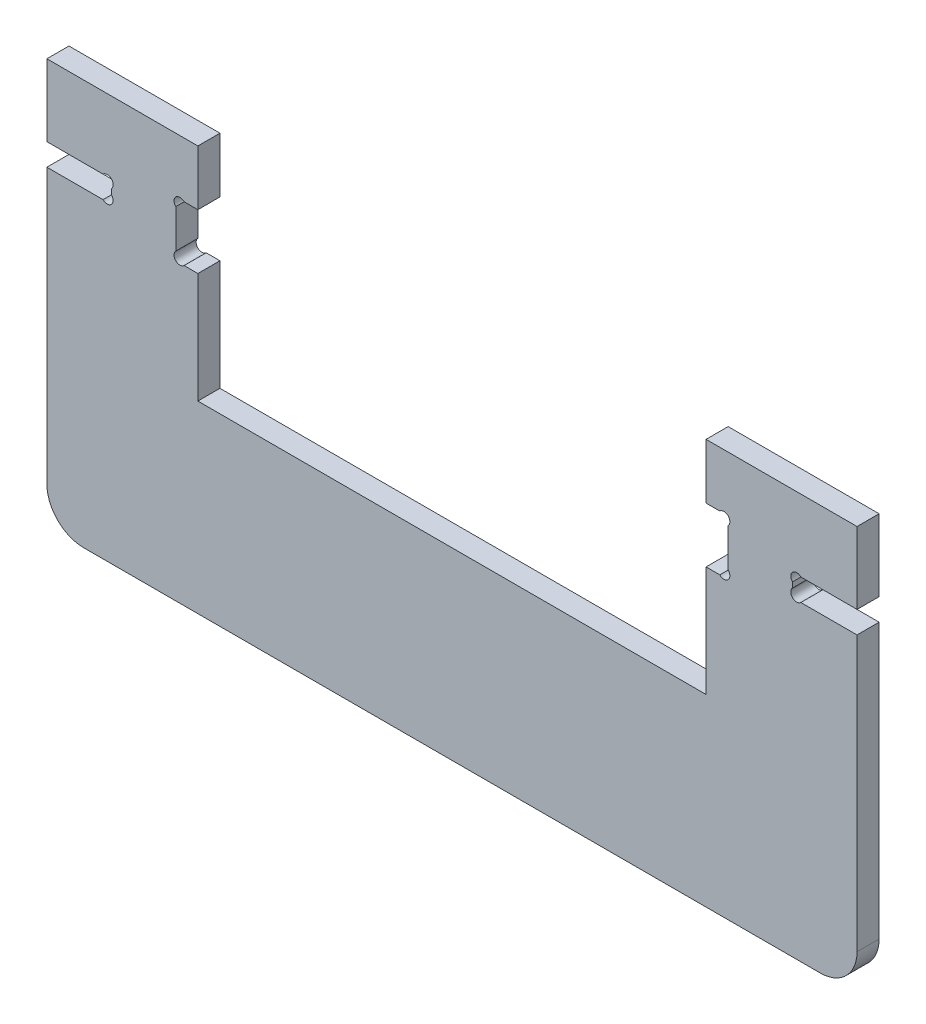
SolidWorks part; units mm, degrees
ref_plane "Plan de face" through (0, 0, 0) normal (0, 0, 1) x (1, 0, 0)
ref_plane "Plan de dessus" through (0, 0, 0) normal (0, 1, 0) x (1, 0, 0)
ref_plane "Plan de droite" through (0, 0, 0) normal (1, 0, 0) x (0, 0, -1)
sketch "Esquisse1" plane through (0, 0, 0) normal (0, 0, 1) x (1, 0, 0)
  line L0 (-10, 0) -> (230, 0) construction
  line L1 (0, -16.234) -> (0, 120) construction
  line L2 (22.1288, 80) -> (50.9911, 80) construction
  line L3 (220, 120) -> (220, -12.4421) construction
  line L4 (22.1288, 50) -> (200.9495, 50) construction
  line L5 (110, -25.3456) -> (110, 158.8084) construction
  line L6 (35, 117.3973) -> (35, -12.4421) construction
  line L7 (41, 114.2601) -> (41, -12.4421) construction
  line L8 (26.2072, 95) -> (48.7951, 95) construction
  line L9 (-34.6546, 110) -> (236.3999, 110) construction
  line L10 (35, 95) -> (43.0807, 86.9193) construction
  line L11 (20, 87.5) -> (44.1754, 87.5) construction
  line L12 (41, 110) -> (41, 95)
  line L13 (41, 95) -> (37.2627, 95)
  line L14 (179, 80) -> (179, 50)
  line L15 (35, 92.7373) -> (35, 82.2627)
  line L16 (182.7373, 80) -> (179, 80)
  line L17 (37.2627, 80) -> (41, 80)
  line L18 (41, 80) -> (41, 50)
  line L19 (185, 92.7373) -> (185, 82.2627)
  line L20 (179, 95) -> (182.7373, 95)
  line L21 (179, 110) -> (179, 95)
  line L22 (41, 50) -> (179, 50)
  line L23 (179, 110) -> (220, 110)
  line L24 (0, 110) -> (41, 110)
  line L25 (0, 110) -> (0, 90.5)
  line L26 (10, 0) -> (210, 0)
  line L27 (220, 110) -> (220, 90.5)
  line L28 (17.52, 71.949) -> (17.52, 124.8953) construction
  line L29 (-2.2278, 84.5) -> (22.6033, 84.5) construction
  line L30 (-2.2278, 90.5) -> (22.6033, 90.5) construction
  line L31 (17.52, 90.5) -> (7.9505, 80.9305) construction
  line L32 (0, 84.5) -> (0, 10)
  line L33 (0, 90.5) -> (15.2573, 90.5)
  line L34 (220, 90.5) -> (204.7427, 90.5)
  line L35 (0, 84.5) -> (15.2573, 84.5)
  line L36 (17.52, 88.2373) -> (17.52, 86.7627)
  line L37 (202.48, 88.2373) -> (202.48, 86.7627)
  line L38 (220, 84.5) -> (204.7427, 84.5)
  line L39 (220, 84.5) -> (220, 10)
  arc A0 (37.2627, 95) -> (35, 92.7373) centre (36.1314, 93.8686) ccw
  arc A1 (37.2627, 80) -> (35, 82.2627) centre (36.1314, 81.1314) cw
  arc A2 (182.7373, 80) -> (185, 82.2627) centre (183.8686, 81.1314) ccw
  arc A3 (182.7373, 95) -> (185, 92.7373) centre (183.8686, 93.8686) cw
  arc A4 (0, 10) -> (10, 0) centre (10, 10) ccw
  arc A5 (210, 0) -> (220, 10) centre (210, 10) ccw
  arc A6 (17.52, 88.2373) -> (15.2573, 90.5) centre (16.3886, 89.3686) ccw
  arc A7 (17.52, 86.7627) -> (15.2573, 84.5) centre (16.3886, 85.6314) cw
  arc A8 (202.48, 88.2373) -> (204.7427, 90.5) centre (203.6114, 89.3686) cw
  arc A9 (202.48, 86.7627) -> (204.7427, 84.5) centre (203.6114, 85.6314) ccw
  point P53 (220, 0)
  dimension "D4" = 7.5
  dimension "D5" = 10
  dimension "D1" = 75
  dimension "D2" = 6
  dimension "D3" = 45
  dimension "D6" = 3
  dimension "D7" = 6
  dimension "D8" = 45
extrude "Extrusion1" add sketch "Esquisse1" along normal blind 6
